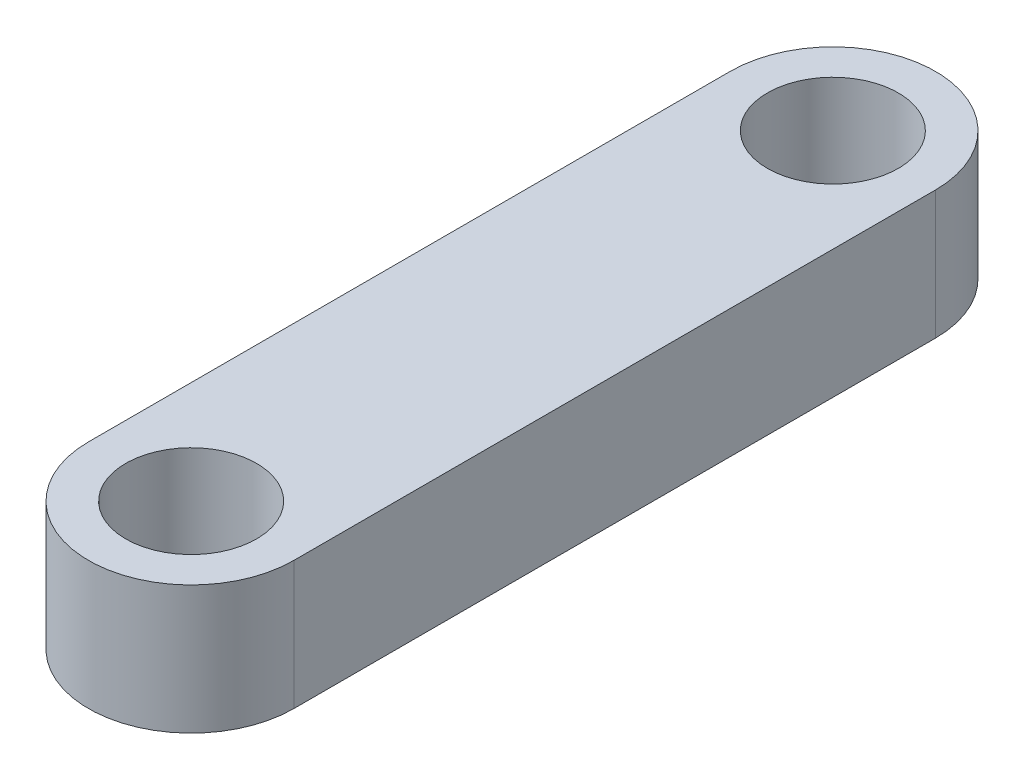
SolidWorks part; units mm, degrees
ref_plane "Front Plane" through (0, 0, 0) normal (0, 0, 1) x (1, 0, 0)
ref_plane "Top Plane" through (0, 0, 0) normal (0, 1, 0) x (1, 0, 0)
ref_plane "Right Plane" through (0, 0, 0) normal (1, 0, 0) x (0, 0, -1)
sketch "Sketch1" plane through (0, 0, 0) normal (0, 1, 0) x (1, 0, 0)
  line L2 (-4, -12.5) -> (-4, 12.5)
  line L4 (4, -12.5) -> (4, 12.5)
  line L5 (-4, -12.5) -> (4, 12.5) construction
  line L6 (-4, 12.5) -> (4, -12.5) construction
  arc A0 (4, 12.5) -> (-4, 12.5) centre (0, 12.5) ccw
  arc A1 (-4, -12.5) -> (4, -12.5) centre (0, -12.5) ccw
  point P0 (0, 0)
  dimension "D2" = 4
  dimension "D1" = 25
extrude "Boss-Extrude1" add sketch "Sketch1" along normal blind 5
ref_plane "Plane1" through (0, 5, 0) normal (0, 1, 0) x (1, 0, 0)
sketch "Sketch2" plane through (0, 5, 0) normal (0, 1, 0) x (1, 0, 0)
  circle A4 centre (0, 12.5) radius 2.55
  circle A5 centre (0, -12.5) radius 2.55
  dimension "D1" = 5.1
extrude "Cut-Extrude2" cut sketch "Sketch2" against normal through all
